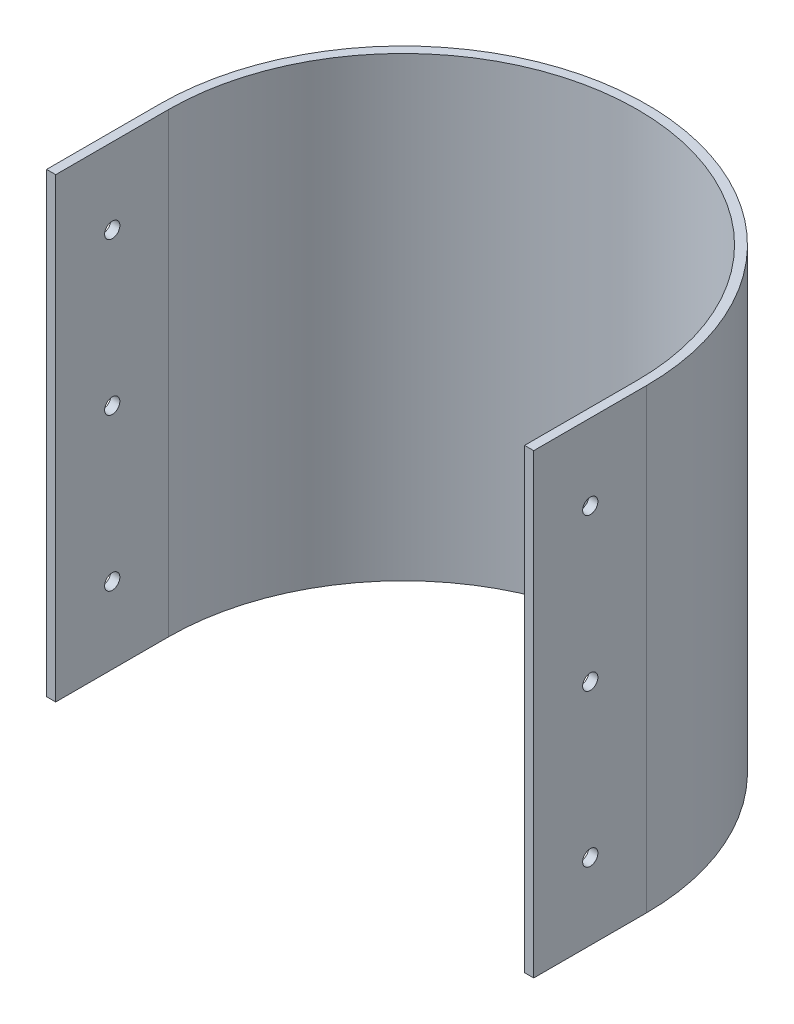
SolidWorks part; units mm, degrees
ref_plane "Front Plane" through (0, 0, 0) normal (0, 0, 1) x (1, 0, 0)
ref_plane "Top Plane" through (0, 0, 0) normal (0, 1, 0) x (1, 0, 0)
ref_plane "Right Plane" through (0, 0, 0) normal (1, 0, 0) x (0, 0, -1)
sketch "Sketch1" plane through (0, 0, 0) normal (0, 1, 0) x (1, 0, 0)
  line L0 (-80.8851, 0) -> (-80.8851, -37.0674)
  line L1 (-80.8851, -37.0674) -> (-77.8851, -37.0674)
  line L2 (-77.8851, -37.0674) -> (-77.8851, 0)
  line L3 (76.1149, 0) -> (76.1149, -37.0674)
  line L4 (76.1149, -37.0674) -> (79.1149, -37.0674)
  line L5 (79.1149, -37.0674) -> (79.1149, 0)
  arc A0 (-77.8851, 0) -> (76.1149, 0) centre (-0.8851, 0) cw
  arc A1 (-80.8851, 0) -> (79.1149, 0) centre (-0.8851, 0) cw
  dimension "D1" = 154
  dimension "D2" = 3
  dimension "D3" = 37.0674
extrude "Boss-Extrude1" add sketch "Sketch1" along normal blind 150
sketch "Sketch2" plane through (79.1149, 0, 0) normal (1, 0, 0) x (0, 0, -1)
  line L0 (-37.0674, 150) -> (0, 150) construction
  line L2 (-37.0674, 0) -> (0, 0) construction
  line L3 (0, 150) -> (0, 0) construction
  circle A0 centre (-18.5, 125) radius 2.5
  circle A1 centre (-18.5, 75) radius 2.5
  circle A2 centre (-18.5, 25) radius 2.5
  point P8 (0, 0)
  point P9 (0, 0)
  point P10 (-19.8935, 25.7578)
  point P11 (-19.8935, 125)
  point P12 (0, 0)
  point P13 (0, 0)
  point P14 (7.9255, 30.1417)
  point P15 (0, 0)
  dimension "D6" = 5
  dimension "D1" = 50
  dimension "D2" = 25
  dimension "D3" = 25
  dimension "D4" = 50
  dimension "D5" = 18.5
extrude "Cut-Extrude1" cut sketch "Sketch2" against normal through all
